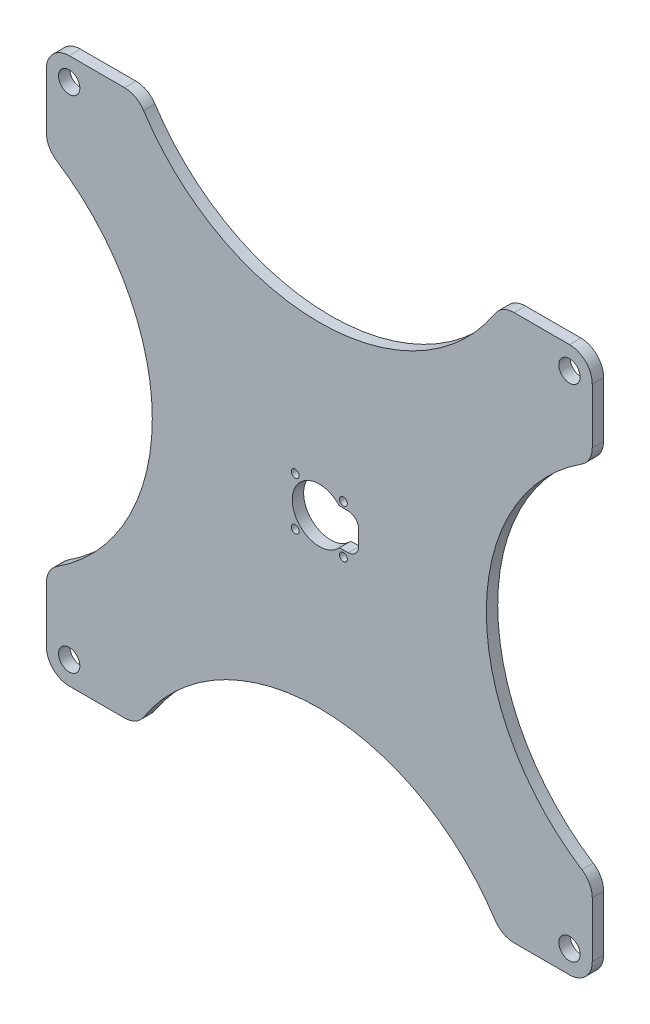
SolidWorks part; units mm, degrees
ref_plane "Front Plane" through (0, 0, 0) normal (0, 0, 1) x (1, 0, 0)
ref_plane "Top Plane" through (0, 0, 0) normal (0, 1, 0) x (1, 0, 0)
ref_plane "Right Plane" through (0, 0, 0) normal (1, 0, 0) x (0, 0, -1)
sketch "Sketch3" plane through (0, 0, 0) normal (0, 0, 1) x (1, 0, 0)
  line L1 (-76.2, -76.2) -> (76.2, -76.2)
  line L2 (-76.2, -76.2) -> (-76.2, 76.2)
  line L3 (-76.2, 76.2) -> (76.2, 76.2)
  line L4 (76.2, -76.2) -> (76.2, 76.2)
  line L5 (-76.2, -76.2) -> (76.2, 76.2) construction
  line L6 (-76.2, 76.2) -> (76.2, -76.2) construction
  point P0 (0, 0)
  dimension "D1" = 152.4
extrude "Boss-Extrude3" add sketch "Sketch3" along normal blind 3.175
sketch "Sketch13" plane through (0.1069, -2.0309, 3.175) normal (0, 0, 1) x (1, 0, 0)
  line L0 (10.8931, 2.1056) -> (16.2467, 2.1056) construction
  line L1 (-76.3069, 78.2309) -> (76.0931, -74.1691) construction
  line L4 (5.4833, 7.1056) -> (10.8931, 7.1056)
  line L5 (10.8931, -2.8944) -> (10.8931, 7.1056)
  line L7 (5.4833, -3.0438) -> (10.8931, -2.8944)
  line L16 (-76.3069, -74.1691) -> (76.0931, 78.2309) construction
  arc A1 (5.4833, 7.1056) -> (5.4833, -3.0438) centre (-0.1069, 2.0309) ccw
  dimension "D1" = 5.5902
  dimension "D4" = 10
  dimension "D3" = 7.55
  dimension "D2" = 5.5902
  dimension "D5" = 11
extrude "Motor Cut Out" cut sketch "Sketch13" against normal through all
sketch "Sketch20" plane through (0, 0, 3.175) normal (0, 0, 1) x (1, 0, 0)
  line L1 (-69.83, -69.83) -> (69.83, -69.83) construction
  line L2 (-69.83, -69.83) -> (-69.83, 69.83) construction
  line L3 (-69.83, 69.83) -> (69.83, 69.83) construction
  line L4 (69.83, -69.83) -> (69.83, 69.83) construction
  line L5 (-69.83, -69.83) -> (69.83, 69.83) construction
  line L6 (-69.83, 69.83) -> (69.83, -69.83) construction
  circle A0 centre (-69.83, 69.83) radius 2.9718
  circle A1 centre (69.83, 69.83) radius 2.9718
  circle A2 centre (69.83, -69.83) radius 2.9718
  circle A3 centre (-69.83, -69.83) radius 2.9718
  point P0 (0, 0)
  point P11 (0, 0)
  dimension "D1" = 4
  dimension "D2" = 139.66
  dimension "D3" = 5.9436
extrude "Bolt Holes" cut sketch "Sketch20" against normal through all both and the other way through all
sketch "Sketch21" plane through (0, 0, 3.175) normal (0, 0, 1) x (1, 0, 0)
  line L1 (-39.6561, -36.877) -> (39.6561, -36.877)
  line L2 (-39.6561, -36.877) -> (-39.6561, 36.877)
  line L3 (-39.6561, 36.877) -> (39.6561, 36.877)
  line L4 (39.6561, -36.877) -> (39.6561, 36.877)
  line L5 (-39.6561, -36.877) -> (39.6561, 36.877) construction
  line L6 (-39.6561, 36.877) -> (39.6561, -36.877) construction
  point P0 (0, 0)
ref_plane "Mirror" through (0, 0, 0) normal (0.7071, -0.7071, 0) x (-0.7071, -0.7071, 0)
sketch "Sketch25" plane through (0, 0, 3.175) normal (0, 0, 1) x (1, 0, 0)
  line L0 (-76.2, 76.2) -> (-76.2, -76.2) construction
  line L1 (76.2, 76.2) -> (-76.2, 76.2) construction
  line L2 (-76.2, -76.2) -> (76.2, -76.2) construction
  line L3 (-76.2, 50.8) -> (-76.2, -50.8)
  arc A0 (-76.2, 50.8) -> (-76.2, -50.8) centre (-105.0489, 0) cw
  dimension "D3" = 58.42
  dimension "D1" = 25.4
  dimension "D2" = 25.4
extrude "Edge cut out" cut sketch "Sketch25" against normal up to surface (3.175 mm away) up to face at (-66.8582, -69.83, 0)
fillet "Fillet2" radius 6.35 4 edges at (-76.2, -76.2, 1.5875) (-76.2, -50.8, 1.5875) (-76.2, 50.8, 1.5875) (-76.2, 76.2, 1.5875)
ref_plane "Plane3" through (0, 0, 0) normal (-0.7071, -0.7071, 0) x (-0.7071, 0.7071, 0)
mirror "Mirror4" about plane through (0, 0, 0) normal (0.7071, -0.7071, 0) of "Edge cut out"
mirror "Mirror5" about plane through (0, 0, 0) normal (-0.7071, -0.7071, 0) of "Mirror4", "Edge cut out"
fillet "Fillet3" radius 6.35 6 edges at (76.2, 76.2, 1.5875) (76.2, 50.8, 1.5875) (76.2, -50.8, 1.5875) (76.2, -76.2, 1.5875) (50.8, -76.2, 1.5875) (-50.8, -76.2, 1.5875)
fillet "Fillet4" radius 6.35 2 edges at (-50.8, 76.2, 1.5875) (50.8, 76.2, 1.5875)
fillet "Fillet12" radius 3 2 edges at (11, 5.0747, 1.5875) (11, -4.9253, 1.5875)
sketch "Sketch27" plane through (0, 0, 3.175) normal (0, 0, 1) x (1, 0, 0)
  line L3 (-6.72, -6.72) -> (6.72, -6.72) construction
  line L4 (-6.72, -6.72) -> (-6.72, 6.72) construction
  line L5 (-6.72, 6.72) -> (6.72, 6.72) construction
  line L6 (6.72, -6.72) -> (6.72, 6.72) construction
  line L7 (-6.72, -6.72) -> (6.72, 6.72) construction
  line L8 (-6.72, 6.72) -> (6.72, -6.72) construction
  circle A5 centre (6.72, -6.72) radius 1.1
  circle A6 centre (6.72, 6.72) radius 1.1
  circle A9 centre (-6.72, 6.72) radius 1.1
  circle A10 centre (-6.72, -6.72) radius 1.1
  point P0 (0, 0)
  dimension "D1" = 13.44
  dimension "D8" = 2.2
extrude "Motor screws hole" cut sketch "Sketch27" against normal through all
